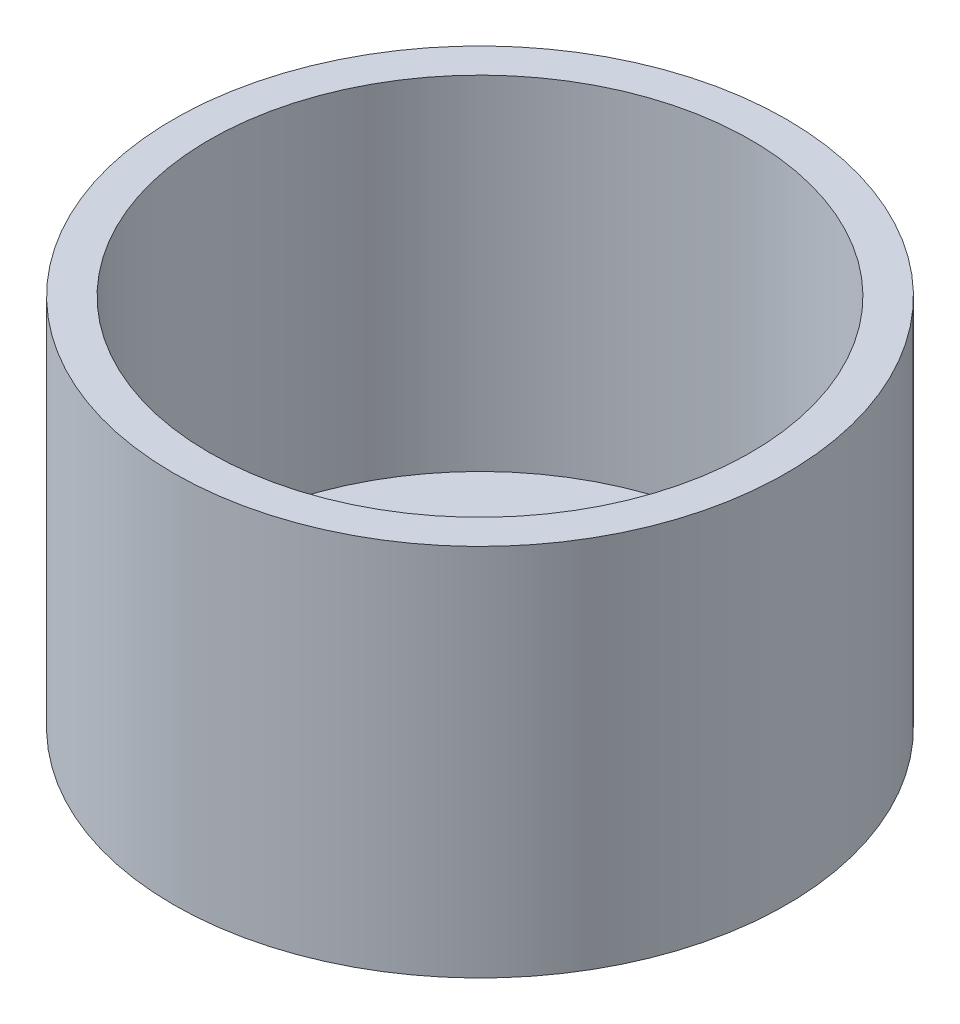
SolidWorks part; units mm, degrees
ref_plane "Front Plane" through (0, 0, 0) normal (0, 0, 1) x (1, 0, 0)
ref_plane "Top Plane" through (0, 0, 0) normal (0, 1, 0) x (1, 0, 0)
ref_plane "Right Plane" through (0, 0, 0) normal (1, 0, 0) x (0, 0, -1)
sketch "Sketch1" plane through (0, 0, 0) normal (0, 1, 0) x (1, 0, 0)
  circle A0 centre (0, 0) radius 51.0286
  circle A1 centre (0, 0) radius 45.085
  dimension "D1" = 90.17
  dimension "D2" = 5.9436
extrude "Boss-Extrude1" add sketch "Sketch1" along normal blind 57.15
sketch "Sketch2" plane through (0, 0, 0) normal (0, -1, 0) x (1, 0, 0)
  circle A0 centre (0, 0) radius 51.0286
  circle A1 centre (0, 0) radius 51.0286 construction
extrude "Boss-Extrude2" add sketch "Sketch2" along normal blind 5.08
sketch "Sketch3" plane through (0, -5.08, 0) normal (0, -1, 0) x (-1, 0, 0)
  line L0 (27.1486, 0) -> (-29.3775, 0) construction
  line L1 (0, -23.2791) -> (0, 21.7313) construction
  circle A0 centre (14.05, -7.35) radius 1
  circle A1 centre (14.05, -12.35) radius 1
  circle A2 centre (19.05, -12.35) radius 1
  circle A3 centre (19.05, -7.35) radius 1
  circle A4 centre (19.05, 7.35) radius 1
  circle A5 centre (19.05, 12.35) radius 1
  circle A6 centre (14.05, 12.35) radius 1
  circle A7 centre (-14.05, 12.35) radius 1
  circle A8 centre (-14.05, 7.35) radius 1
  circle A9 centre (-19.05, 12.35) radius 1
  circle A10 centre (-19.05, 7.35) radius 1
  circle A11 centre (-19.05, -7.35) radius 1
  circle A12 centre (-14.05, -7.35) radius 1
  circle A13 centre (-14.05, -12.35) radius 1
  circle A14 centre (-19.05, -12.35) radius 1
  circle A15 centre (14.05, 7.35) radius 1
  dimension "D21" = 2
  dimension "D22" = 2
  dimension "D23" = 2
  dimension "D24" = 2
  dimension "D25" = 2
  dimension "D26" = 2
  dimension "D27" = 2
  dimension "D28" = 2
  dimension "D29" = 2
  dimension "D30" = 2
  dimension "D31" = 2
  dimension "D32" = 2
  dimension "D33" = 2
  dimension "D34" = 2
  dimension "D35" = 2
  dimension "D36" = 2
  dimension "D1" = 5
  dimension "D2" = 5
  dimension "D3" = 5
  dimension "D4" = 5
  dimension "D5" = 28.1
  dimension "D6" = 14.7
  dimension "D7" = 5
  dimension "D8" = 5
  dimension "D9" = 5
  dimension "D10" = 5
  dimension "D11" = 28.1
  dimension "D12" = 5
  dimension "D13" = 5
  dimension "D14" = 5
  dimension "D15" = 5
  dimension "D16" = 5
  dimension "D17" = 14.7
  dimension "D18" = 5
  dimension "D19" = 5
  dimension "D20" = 5
  dimension "D37" = 14.05
  dimension "D38" = 14.05
  dimension "D39" = 7.35
  dimension "D40" = 7.35
extrude "Cut-Extrude1" cut sketch "Sketch3" against normal through all both and the other way through all
